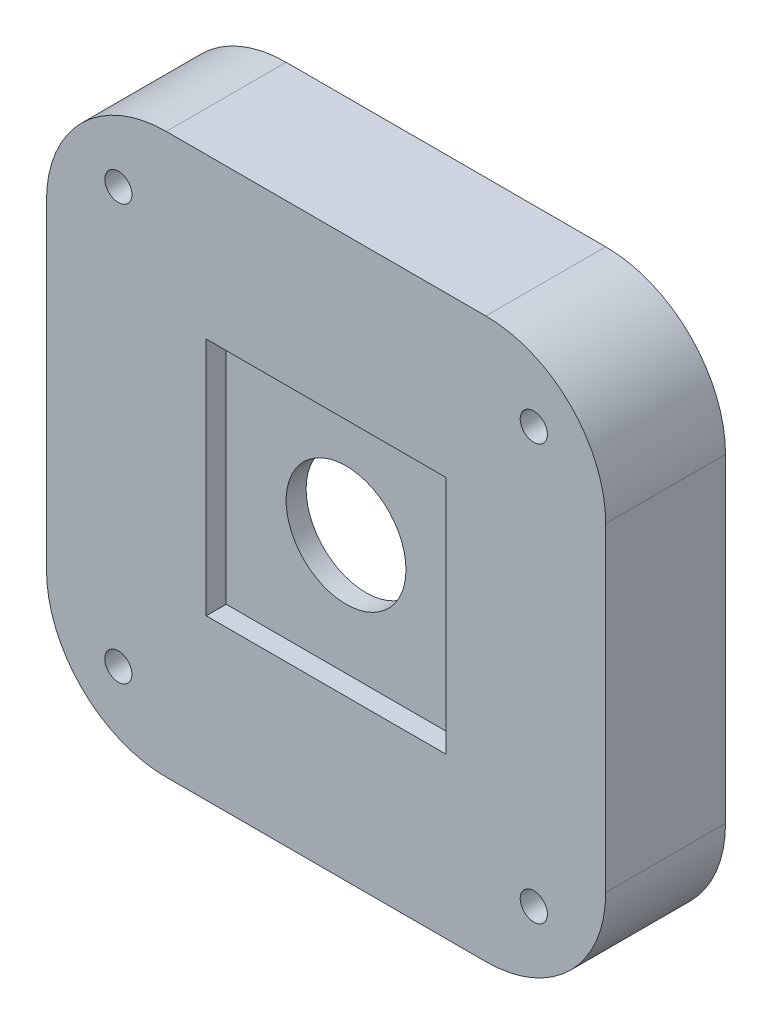
SolidWorks part; units mm, degrees
ref_plane "Front Plane" through (0, 0, 0) normal (0, 0, 1) x (1, 0, 0)
ref_plane "Top Plane" through (0, 0, 0) normal (0, 1, 0) x (1, 0, 0)
ref_plane "Right Plane" through (0, 0, 0) normal (1, 0, 0) x (0, 0, -1)
sketch "Sketch1" plane through (0, 0, 0) normal (0, 0, 1) x (1, 0, 0)
  line L1 (35, 35) -> (-35, 35)
  line L2 (35, 35) -> (35, -35)
  line L3 (35, -35) -> (-35, -35)
  line L4 (-35, 35) -> (-35, -35)
  line L5 (35, 35) -> (-35, -35) construction
  line L6 (35, -35) -> (-35, 35) construction
  point P0 (0, 0)
  dimension "D1" = 70
  dimension "D2" = 70
extrude "Boss-Extrude1" add sketch "Sketch1" along normal blind 15
fillet "Fillet1" radius 15 4 edges at (35, -35, 7.5) (-35, -35, 7.5) (-35, 35, 7.5) (35, 35, 7.5)
hole_wizard "M3 Clearance Hole1" positions "Sketch2" profile "Sketch3" hole size "M3" standard "ISO" end condition through all
sketch "Sketch2" plane through (0, 0, 15) normal (0, 0, 1) x (1, 0, 0)
  line L0 (20, 35) -> (-20, 35) construction
  line L1 (-35, 20) -> (-35, -20) construction
  line L2 (35, -20) -> (35, 20) construction
  line L3 (-20, -35) -> (20, -35) construction
  point P0 (-26, -26)
  point P2 (26, -26)
  point P4 (26, 26)
  point P6 (-26, 26)
  dimension "D1" = 9
  dimension "D2" = 9
  dimension "D3" = 52
  dimension "D4" = 52
  dimension "D5" = 52
  dimension "D6" = 9
  dimension "D7" = 9
  dimension "D8" = 9
sketch "Sketch3" plane through (-26, -26, 15) normal (1, 0, 0) x (0, -1, 0)
  line L0 (0, 0) -> (0, 15)
  line L1 (0, 15) -> (1.7, 15)
  line L2 (1.7, 15) -> (1.7, 0)
  line L5 (1.7, 0) -> (0, 0)
  line L11 (0, -6.35) -> (0, 107.95) construction
  dimension "Thru Hole Dia." = 3.4
  dimension "Thru Hole Depth" = 15
sketch "Sketch4" plane through (0, 0, 15) normal (0, 0, 1) x (1, 0, 0)
  circle A0 centre (0, 0) radius 7.5
  dimension "D1" = 15
extrude "Cut-Extrude1" cut sketch "Sketch4" against normal through all
sketch "Sketch5" plane through (0, 0, 15) normal (0, 0, 1) x (1, 0, 0)
  line L1 (15, -15) -> (-15, -15)
  line L2 (15, -15) -> (15, 15)
  line L3 (15, 15) -> (-15, 15)
  line L4 (-15, -15) -> (-15, 15)
  line L5 (15, -15) -> (-15, 15) construction
  line L6 (15, 15) -> (-15, -15) construction
  point P0 (0, 0)
  dimension "D1" = 30
  dimension "D2" = 30
extrude "Cut-Extrude2" cut sketch "Sketch5" against normal blind 2.5
sketch "Sketch6" plane through (0, 0, 0) normal (0, 0, -1) x (-1, 0, 0)
  line L1 (-22.5, 22.5) -> (22.5, 22.5)
  line L2 (-22.5, 22.5) -> (-22.5, -22.5)
  line L3 (-22.5, -22.5) -> (22.5, -22.5)
  line L4 (22.5, 22.5) -> (22.5, -22.5)
  line L5 (-22.5, 22.5) -> (22.5, -22.5) construction
  line L6 (-22.5, -22.5) -> (22.5, 22.5) construction
  point P0 (0, 0)
  dimension "D1" = 45
  dimension "D2" = 45
extrude "Cut-Extrude3" cut sketch "Sketch6" against normal blind 10
